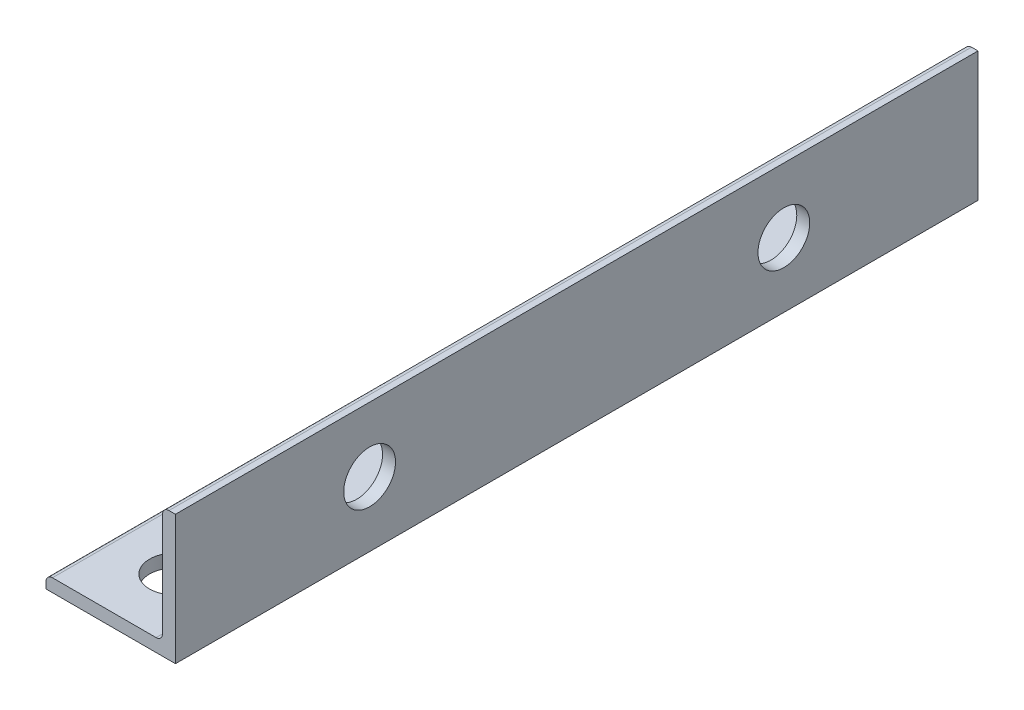
SolidWorks part; units mm, degrees
material "McMaster 6061-T6"
ref_plane "Front Plane" through (0, 0, 0) normal (0, 0, 1) x (1, 0, 0)
ref_plane "Top Plane" through (0, 0, 0) normal (0, 1, 0) x (1, 0, 0)
ref_plane "Right Plane" through (0, 0, 0) normal (1, 0, 0) x (0, 0, -1)
sketch "Sketch2" plane through (0, 0, 0) normal (0, 0, 1) x (1, 0, 0)
  line L0 (-7.9375, 0) -> (7.9375, 0)
  line L1 (7.9375, 0) -> (7.9375, 15.875)
  line L2 (7.9375, 15.875) -> (6.35, 15.875) construction
  line L3 (6.35, 15.0813) -> (6.35, 2.3812)
  line L4 (5.5563, 1.5875) -> (-7.1438, 1.5875)
  line L5 (-7.9375, 0) -> (-7.9375, 1.5875) construction
  line L6 (7.1438, 15.875) -> (7.9375, 15.875)
  line L7 (-7.9375, 0.7937) -> (-7.9375, 0)
  arc A0 (6.35, 15.0813) -> (7.1438, 15.875) centre (7.1438, 15.0813) cw
  arc A1 (-7.9375, 0.7937) -> (-7.1438, 1.5875) centre (-7.1438, 0.7937) cw
  arc A2 (6.35, 2.3812) -> (5.5563, 1.5875) centre (5.5563, 2.3812) cw
  dimension "Vert" = 15.875
  dimension "Horz" = 15.875
  dimension "Thickness" = 1.5875
extrude "Boss-Extrude1" add sketch "Sketch2" along normal mid plane 98.425
ref_plane "Contact Plane 1" through (0, 1.5875, 0) normal (0, 1, 0) x (1, 0, 0)
ref_plane "Contact Plane 2" through (6.35, 0, 0) normal (-1, 0, 0) x (0, 0, 1)
sketch "Sketch3" plane through (7.9375, 0, 0) normal (1, 0, 0) x (0, 0, -1)
  line L0 (25.4, 7.9375) -> (-25.4, 7.9375)
  line L1 (-49.2125, 15.875) -> (49.2125, 15.875) construction
  line L2 (-49.2125, 15.875) -> (-49.2125, 0) construction
  line L3 (-49.2125, 0) -> (49.2125, 0) construction
  line L4 (49.2125, 15.875) -> (49.2125, 0) construction
  circle A0 centre (-25.4, 7.9375) radius 3.175
  circle A1 centre (25.4, 7.9375) radius 3.175
  point P6 (49.2125, 7.9375)
  point P10 (0, 15.875)
  point P13 (0, 7.9375)
  dimension "D1" = 6.35
  dimension "D2" = 50.8
extrude "Cut-Extrude1" cut sketch "Sketch3" against normal through all
sketch "Sketch4" plane through (0, 0, 0) normal (0, -1, 0) x (1, 0, 0)
  line L0 (0, 41.275) -> (0, -41.275) construction
  line L1 (-7.9375, -49.2125) -> (7.9375, -49.2125) construction
  line L3 (7.9375, 49.2125) -> (7.9375, -49.2125) construction
  line L4 (0, 41.275) -> (7.9375, 41.275) construction
  line L6 (0, 41.275) -> (0, 49.2125) construction
  line L7 (-7.9375, 49.2125) -> (7.9375, 49.2125) construction
  circle A0 centre (0, -41.275) radius 3.175
  circle A1 centre (0, 41.275) radius 3.175
  point P4 (0, 0)
  point P9 (0, -49.2125)
  point P14 (7.9375, 0)
  dimension "D1" = 6.35
extrude "Cut-Extrude2" cut sketch "Sketch4" against normal up to next
